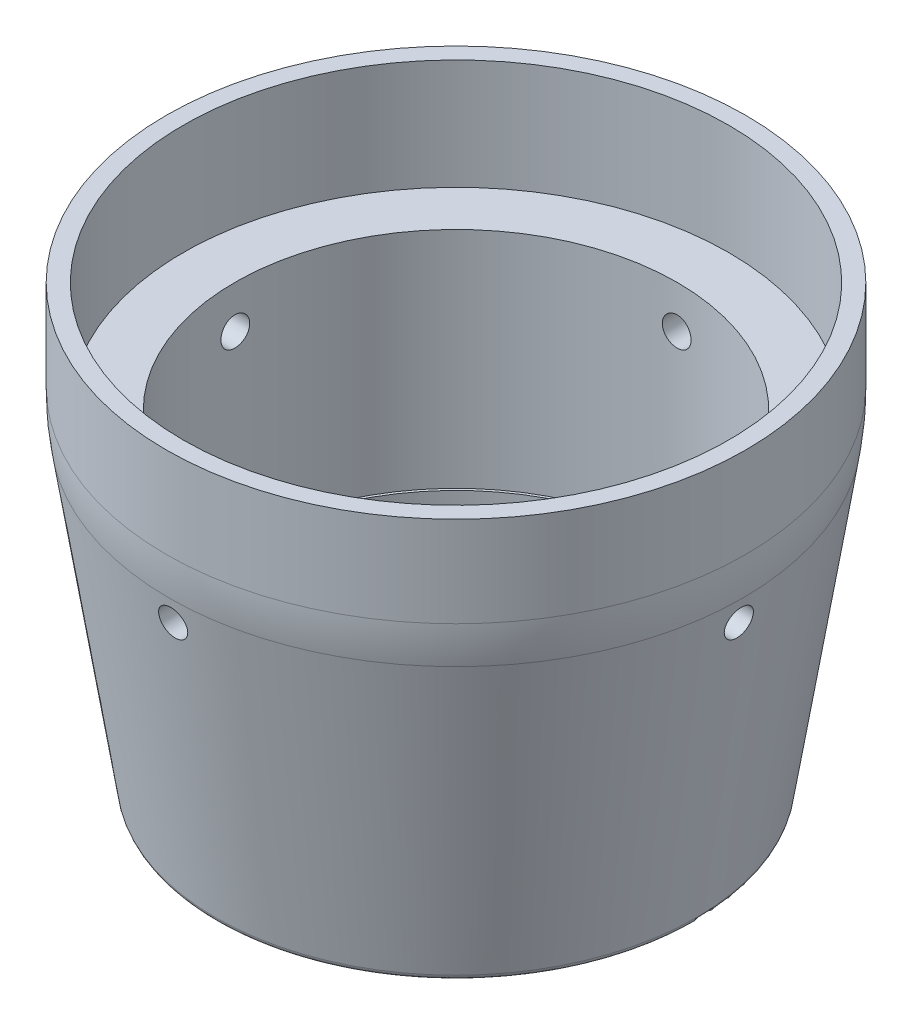
SolidWorks part; units mm, degrees
material "6061-T6 (SS)"
ref_plane "Front Plane" through (0, 0, 0) normal (0, 0, 1) x (1, 0, 0)
ref_plane "Top Plane" through (0, 0, 0) normal (0, 1, 0) x (1, 0, 0)
ref_plane "Right Plane" through (0, 0, 0) normal (1, 0, 0) x (0, 0, -1)
sketch "Sketch2" plane through (0, 0, 0) normal (0, 0, 1) x (1, 0, 0)
  line L8 (22.0472, -22.4282) -> (22.0472, -0.0762)
  line L10 (28.8925, 10.922) -> (28.8925, -0.0762)
  line L11 (28.8925, -0.0762) -> (23.8252, -32.512)
  line L12 (23.8252, -32.512) -> (21.7932, -32.512)
  line L13 (21.7932, -32.512) -> (21.7932, -22.4282)
  line L14 (22.0472, -0.0762) -> (27.1907, -0.0762)
  line L18 (21.7932, -22.4282) -> (22.0472, -22.4282)
  line L19 (27.1907, -0.0762) -> (27.1907, 10.922)
  line L20 (-28.8925, 10.922) -> (28.8925, 10.922) construction
  line L21 (27.1907, 10.922) -> (28.8925, 10.922)
  line L22 (21.717, -32.512) -> (21.717, -22.352) construction
  line L23 (21.971, -22.352) -> (21.971, 7.62) construction
  line L24 (-21.971, -22.352) -> (21.971, -22.352) construction
  line L25 (-27.1145, 0) -> (27.1145, 0) construction
  line L27 (27.1145, 0) -> (27.1145, 10.922) construction
  line L28 (-21.717, -32.512) -> (21.717, -32.512) construction
  dimension "D1" = 0.0762
  dimension "D2" = 0.0762
  dimension "D3" = 0.0762
  dimension "D4" = 0.0762
  dimension "D5" = 0.0762
  dimension "D6" = 2.032
ref_axis "Axis1" through (0, -34.5451, 0) along (0, 1, 0)
revolve "Revolve1" add sketch "Sketch2" angle 360 about axis through (0, -34.5451, 0) along (0, 1, 0)
ref_plane "Plane1" through (0, 0, 28.8925) normal (0, 0, 1) x (1, 0, 0)
sketch "Sketch3" plane through (0, 0, 28.8925) normal (0, 0, 1) x (1, 0, 0)
  line L0 (0, -34.5451) -> (0, 13.0871) construction
  line L2 (28.8925, 10.922) -> (-28.8925, 10.922) construction
  point P0 (0, -4.318)
  dimension "D1" = 15.24
hole_wizard "#6-40 Tapped Hole1" positions "Sketch5" profile "Sketch7" tap size "#6-40" standard "ANSI Inch"
sketch "Sketch5" plane through (0, 0, 28.8925) normal (0, 0, 1) x (1, 0, 0)
  point P0 (0, -4.318)
sketch "Sketch7" plane through (0, -4.318, 28.8925) normal (1, 0, 0) x (0, -1, 0)
  line L0 (0, 0) -> (0, 6.8453)
  line L1 (0, 6.8453) -> (1.4351, 6.8453)
  line L2 (1.4351, 6.8453) -> (1.4351, 0)
  line L5 (1.4351, 0) -> (0, 0)
  line L11 (0, -6.35) -> (0, 107.95) construction
  dimension "Thru Tap Drill Dia." = 2.8702
  dimension "Thru Tap Drill Depth" = 6.8453
pattern_circular "CirPattern1" count 4 over 360 about axis through (0, -34.5451, 0) along (0, -1, 0) of "#6-40 Tapped Hole1"
fillet "Fillet1" radius 0.635 1 edges at (0, -32.512, -23.8252)
fillet "Fillet2" radius 25.4 1 edges at (0, -0.0762, -28.8925)
